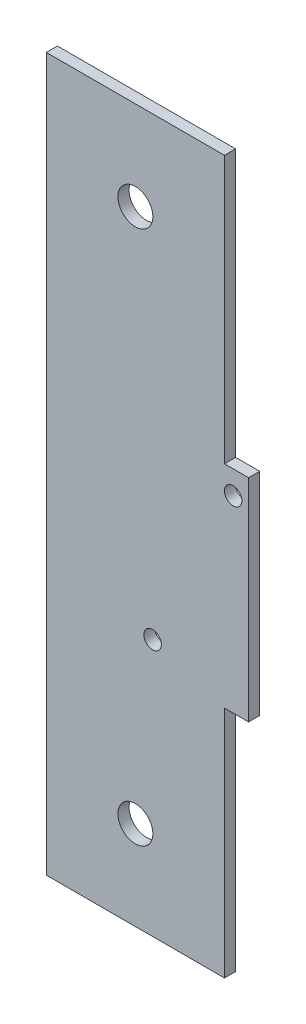
SolidWorks part; units mm, degrees
material "6061-T6 (SS)"
ref_plane "Front Plane" through (0, 0, 0) normal (0, 0, 1) x (1, 0, 0)
ref_plane "Top Plane" through (0, 0, 0) normal (0, 1, 0) x (1, 0, 0)
ref_plane "Right Plane" through (0, 0, 0) normal (1, 0, 0) x (0, 0, -1)
sketch "Sketch1" plane through (0, 0, 0) normal (0, 0, 1) x (1, 0, 0)
  line L0 (0, -50.8) -> (0, -152.4)
  line L2 (0, -152.4) -> (25.4, -152.4)
  line L4 (25.4, -152.4) -> (25.4, -119.0625)
  line L5 (25.4, -119.0625) -> (28.8375, -119.0625)
  line L6 (28.8375, -119.0625) -> (28.8375, -88.9)
  line L7 (28.8375, -88.9) -> (25.4, -88.9)
  line L8 (25.4, -88.9) -> (25.4, -50.8)
  line L9 (25.4, -50.8) -> (0, -50.8)
  line L10 (12.7, -50.8) -> (12.7, -63.5) construction
  line L11 (12.7, -63.5) -> (12.7, -139.7) construction
  line L12 (12.7, -139.7) -> (12.7, -152.4) construction
  circle A0 centre (12.7, -63.5) radius 2.4892
  circle A1 centre (12.7, -139.7) radius 2.4892
  circle A5 centre (15.1552, -115.7383) radius 1.25
  circle A6 centre (26.6386, -92.2302) radius 1.25
  dimension "D4" = 4.9784
  dimension "D1" = 101.6
  dimension "D2" = 30.1625
  dimension "D3" = 12.7
  dimension "D5" = 3.4375
  dimension "D6" = 38.1
extrude "Boss-Extrude1" add sketch "Sketch1" along normal blind 1.5875
equation "\"Thick\"= \"in\""
